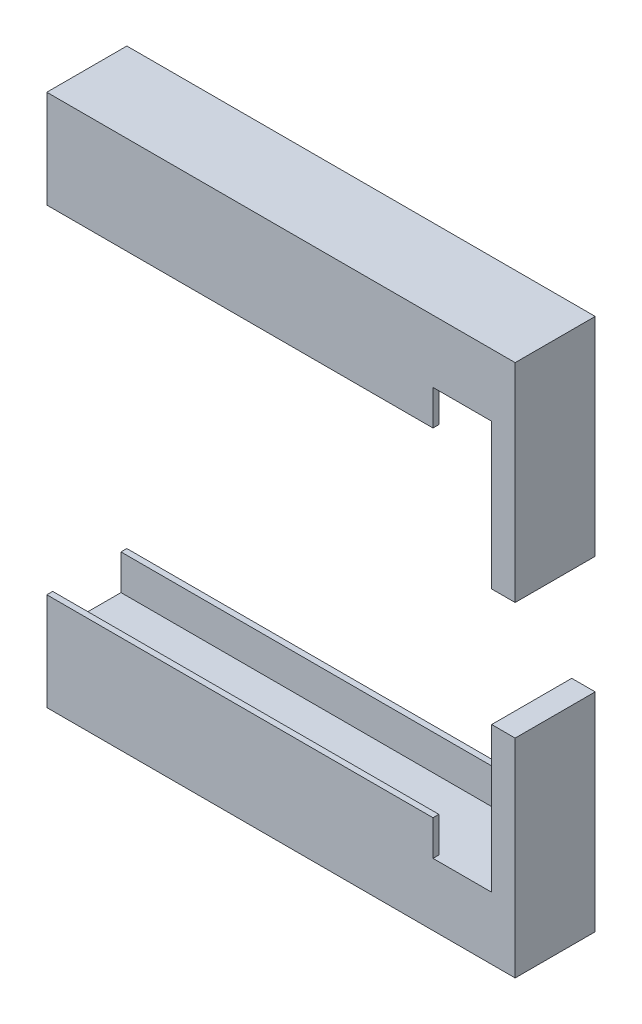
SolidWorks part; units mm, degrees
material "6061-T6 (SS)"
ref_plane "Front Plane" through (0, 0, 0) normal (0, 0, 1) x (1, 0, 0)
ref_plane "Top Plane" through (0, 0, 0) normal (0, 1, 0) x (1, 0, 0)
ref_plane "Right Plane" through (0, 0, 0) normal (1, 0, 0) x (0, 0, -1)
sketch "Sketch1" plane through (0, 0, 0) normal (1, 0, 0) x (0, 0, -1)
  line L1 (0, 0) -> (6.82, 0)
  line L2 (0, 0) -> (0, 45.402)
  line L3 (0, 45.402) -> (6.82, 45.402)
  line L4 (6.82, 0) -> (6.82, 45.402)
  dimension "D1" = 6.82
  dimension "D2" = 45.402
extrude "Boss-Extrude1" add sketch "Sketch1" along normal blind 39.9
sketch "Sketch2" plane through (0, 0, 0) normal (-1, 0, 0) x (0, 0, 1)
  line L0 (-3.41, 45.402) -> (-3.41, 0) construction
  line L1 (-6.82, 45.402) -> (0, 45.402) construction
  line L2 (0, 0) -> (-6.82, 0) construction
  line L3 (-6.82, 0) -> (-6.82, 45.402) construction
  line L4 (-6.32, 5.326) -> (-0.5, 5.326)
  line L5 (-6.32, 5.326) -> (-6.32, 8.326)
  line L6 (-6.32, 40.076) -> (-0.5, 40.076)
  line L7 (-0.5, 5.326) -> (-0.5, 8.326)
  line L8 (-6.32, 5.326) -> (-0.5, 40.076) construction
  line L9 (-6.32, 40.076) -> (-0.5, 5.326) construction
  line L10 (-6.82, 8.326) -> (-6.32, 8.326)
  line L11 (-6.82, 0) -> (-6.82, 45.402) construction
  line L12 (-6.32, 8.326) -> (-0.5, 8.326) construction
  line L13 (-0.5, 8.326) -> (0, 8.326)
  line L14 (0, 45.402) -> (0, 0) construction
  line L15 (-6.82, 22.701) -> (0, 22.701) construction
  line L16 (-0.5, 37.076) -> (0, 37.076)
  line L17 (-6.82, 37.076) -> (-6.32, 37.076)
  line L18 (-6.82, 37.076) -> (-6.82, 22.701)
  line L19 (-6.82, 22.701) -> (-6.82, 8.326)
  line L20 (0, 8.326) -> (0, 37.076)
  line L21 (-0.5, 37.076) -> (-0.5, 40.076)
  line L22 (-6.32, 37.076) -> (-6.32, 40.076)
  point P6 (-3.41, 22.701)
  point P7 (-3.41, 22.701)
  point P12 (-6.82, 22.701)
  dimension "D1" = 0.5
  dimension "D2" = 34.75
  dimension "D3" = 3
extrude "Cut-Extrude1" cut sketch "Sketch2" against normal offset from surface (35.9 mm away) 4 up to face at (39.9, 22.701, -3.41)
sketch "Sketch3" plane through (35.9, 0, 0) normal (-1, 0, 0) x (0, 0, 1)
  line L0 (-6.32, 40.076) -> (-6.32, 37.076) construction
  line L1 (-0.5, 40.076) -> (-6.32, 40.076) construction
  line L2 (-0.5, 37.076) -> (-0.5, 40.076) construction
  line L3 (-0.5, 5.326) -> (-0.5, 8.326) construction
  line L4 (-6.32, 5.326) -> (-0.5, 5.326) construction
  line L5 (-6.32, 8.326) -> (-6.32, 5.326) construction
  line L6 (-6.32, 40.076) -> (-6.32, 37.076)
  line L7 (-0.5, 40.076) -> (-6.32, 40.076)
  line L8 (-0.5, 37.076) -> (-0.5, 40.076)
  line L9 (-0.5, 5.326) -> (-0.5, 8.326)
  line L10 (-6.32, 5.326) -> (-0.5, 5.326)
  line L11 (-6.32, 8.326) -> (-6.32, 5.326)
  line L12 (-6.32, 37.076) -> (-6.32, 8.326) construction
  line L13 (-0.5, 8.326) -> (-0.5, 37.076) construction
  line L14 (-0.5, 37.076) -> (0, 37.076)
  line L15 (0, 37.076) -> (0, 8.326)
  line L16 (0, 37.076) -> (0, 8.326) construction
  line L17 (0, 8.326) -> (-0.5, 8.326)
  line L18 (-6.32, 37.076) -> (-6.82, 37.076)
  line L19 (-6.82, 37.076) -> (-6.82, 8.326)
  line L20 (-6.82, 8.326) -> (-6.32, 8.326)
extrude "Cut-Extrude2" cut sketch "Sketch3" against normal offset from surface (2 mm away) 2 up to face at (39.9, 22.701, -3.41)
sketch "Sketch7" plane through (0, 0, 0) normal (0, 0, 1) x (1, 0, 0)
  line L0 (37.9, 37.076) -> (37.9, 8.326) construction
  line L1 (37.9, 37.076) -> (37.9, 8.326)
  line L2 (37.9, 40.076) -> (0, 40.076) construction
  line L3 (37.9, 40.076) -> (32.9, 40.076)
  line L4 (37.9, 5.326) -> (0, 5.326) construction
  line L5 (37.9, 5.326) -> (32.9, 5.326)
  line L6 (37.9, 37.076) -> (37.9, 40.076)
  line L7 (37.9, 8.326) -> (37.9, 5.326)
  line L8 (32.9, 40.076) -> (32.9, 5.326)
  dimension "D1" = 5
extrude "Cut-Extrude4" cut sketch "Sketch7" against normal through all
hole_wizard "#3-48 Tapped Hole1" positions "Sketch5" profile "Sketch4" tap size "#3-48" standard "ANSI Inch"
sketch "Sketch5" plane through (0, 0, 0) normal (-1, 0, 0) x (0, 0, 1)
  line L0 (-3.41, 45.402) -> (-3.41, 40.076) construction
  line L1 (-6.82, 45.402) -> (0, 45.402) construction
  line L2 (-0.5, 40.076) -> (-6.32, 40.076) construction
  line L3 (-3.41, 40.076) -> (-3.41, 5.326) construction
  line L4 (-6.32, 5.326) -> (-0.5, 5.326) construction
  line L5 (-3.41, 5.326) -> (-3.41, 0) construction
  line L6 (0, 0) -> (-6.82, 0) construction
  point P17 (-3.41, 43.902)
  point P19 (-3.41, 1.5)
  dimension "D1" = 3.826
  dimension "D2" = 3.826
sketch "Sketch4" plane through (0, 1.5, -3.41) normal (0, 1, 0) x (0, 0, 1)
  line L0 (0, 0) -> (0, 8.27)
  line L1 (0, 8.27) -> (0.9969, 7.671)
  line L2 (0.9969, 7.671) -> (0.9969, 0)
  line L5 (0.9969, 0) -> (0, 0)
  line L10 (0, 8.27) -> (-0.997, 7.671) construction
  line L11 (0, -6.35) -> (0, 107.95) construction
  dimension "Tap Drill Dia." = 1.9939
  dimension "Tap Drill Depth" = 7.671
  dimension "Drill Angle" = 118
cosmetic thread "Hole Thread1" parameters "D1"=5.029, "D2"=2.5146
cosmetic thread "Hole Thread2" parameters "D1"=5.029, "D2"=2.5146
sketch "Sketch6" plane through (39.9, 0, 0) normal (1, 0, 0) x (0, 0, -1)
  line L0 (0, 22.701) -> (6.82, 22.701) construction
  line L1 (0, 45.402) -> (0, 0) construction
  line L2 (6.82, 0) -> (6.82, 45.402) construction
  line L4 (6.82, 17.701) -> (0, 17.701)
  line L5 (6.82, 17.701) -> (6.82, 27.701)
  line L6 (6.82, 27.701) -> (0, 27.701)
  line L7 (0, 17.701) -> (0, 27.701)
  line L8 (6.82, 17.701) -> (0, 27.701) construction
  line L9 (6.82, 27.701) -> (0, 17.701) construction
  point P6 (3.41, 22.701)
  point P7 (3.41, 22.701)
  dimension "D1" = 10
extrude "Cut-Extrude3" cut sketch "Sketch6" against normal up to next
